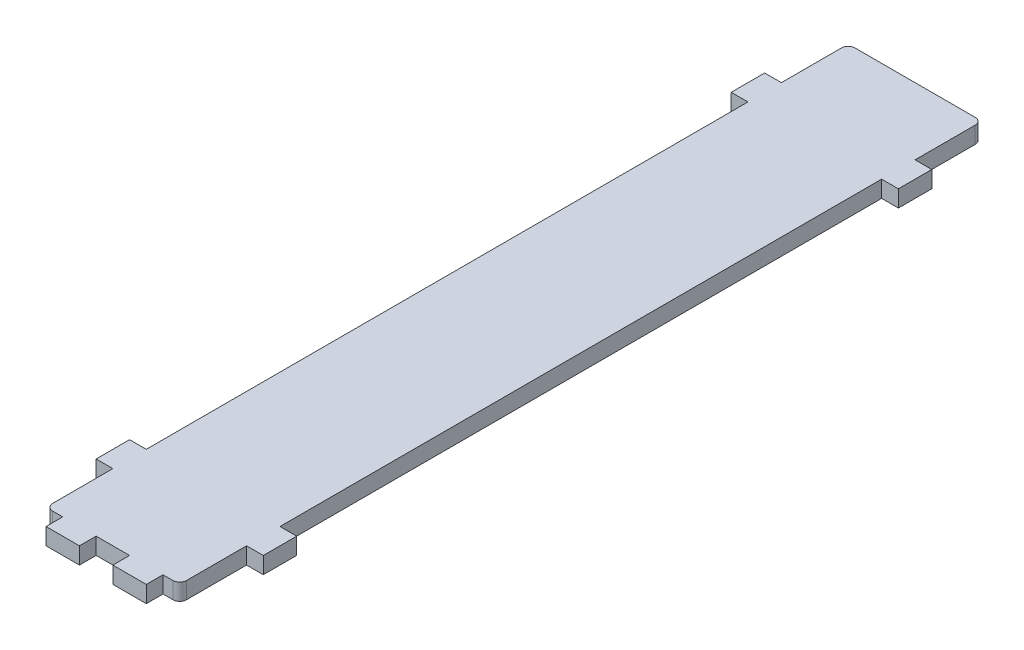
SolidWorks part; units mm, degrees
material "Beech"
ref_plane "Front Plane" through (0, 0, 0) normal (0, 0, 1) x (1, 0, 0)
ref_plane "Top Plane" through (0, 0, 0) normal (0, 1, 0) x (1, 0, 0)
ref_plane "Right Plane" through (0, 0, 0) normal (1, 0, 0) x (0, 0, -1)
sketch "Sketch1" plane through (0, 0, 0) normal (0, 1, 0) x (1, 0, 0)
  line L0 (0, 0) -> (6.35, 0)
  line L1 (6.35, 0) -> (6.35, -6.35)
  line L2 (6.35, -6.35) -> (19.05, -6.35)
  line L3 (19.05, -6.35) -> (19.05, 0)
  line L4 (19.05, 0) -> (31.75, 0)
  line L5 (31.75, 0) -> (31.75, -6.35)
  line L6 (31.75, -6.35) -> (44.45, -6.35)
  line L7 (44.45, -6.35) -> (44.45, 0)
  line L8 (44.45, 0) -> (50.8, 0)
  line L9 (50.8, 0) -> (50.8, 25.4)
  line L10 (50.8, 304.8) -> (0, 304.8)
  line L11 (0, 304.8) -> (0, 279.4)
  line L12 (50.8, 25.4) -> (57.15, 25.4)
  line L13 (57.15, 25.4) -> (57.15, 38.1)
  line L14 (57.15, 38.1) -> (50.8, 38.1)
  line L15 (50.8, 38.1) -> (50.8, 266.7)
  line L16 (50.8, 266.7) -> (57.15, 266.7)
  line L17 (57.15, 266.7) -> (57.15, 279.4)
  line L18 (57.15, 279.4) -> (50.8, 279.4)
  line L19 (50.8, 279.4) -> (50.8, 304.8)
  line L20 (0, 25.4) -> (-6.35, 25.4)
  line L22 (-6.35, 25.4) -> (-6.35, 38.1)
  line L23 (0, 38.1) -> (-6.35, 38.1)
  line L24 (0, 279.4) -> (-6.35, 279.4)
  line L25 (0, 25.4) -> (0, 0)
  line L26 (-6.35, 279.4) -> (-6.35, 266.7)
  line L27 (0, 266.7) -> (-6.35, 266.7)
  line L28 (0, 266.7) -> (0, 38.1)
  dimension "D1" = 12.7
  dimension "D2" = 6.35
  dimension "D3" = 25.4
  dimension "D4" = 25.4
  dimension "D5" = 6.35
  dimension "D6" = 304.8
  dimension "D7" = 50.8
  dimension "D8" = 25.4
  dimension "D9" = 6.35
extrude "Side Plate" add sketch "Sketch1" along normal blind 6.35
fillet "Fillet1" radius 2.54 4 edges at (50.8, 3.175, 0) (50.8, 3.175, -304.8) (0, 3.175, -304.8) (0, 3.175, 0)
equation "\"CageLeftBottomEdge\"=22.11mm"
equation "\"CageLeftTopEdge\"=22.11mm"
equation "\"CageRightBottomEdge\"=21.63mm"
equation "\"CageRightTopEdge\"=21.63mm"
equation "\"CageHeight\"=86.04mm"
equation "\"CageLength\"=73.76mm"
equation "\"CageTopScrewClearance\"=10mm"
equation "\"CageBottomScrewClearance\"=25mm"
equation "\"CageLeftTopDepth\"= 11.65mm"
equation "\"CageLeftBottomDepth\"=11.11mm"
equation "\"CageLeftTopHeight\"=8.56175mm"
equation "\"CageLeftBottomHeight\"=16mm"
equation "\"CageRightTopDepth\"= 11.05mm"
equation "\"CageRightBottomDepth\"=10.58mm"
equation "\"CageRightTopHeight\"=9.6mm"
equation "\"CageRightBottomHeight\"=15.49mm"
equation "\"CageLeftTopChannelDepth\"=2.41908mm"
equation "\"CageLeftBottomChannelDepth\"=2.588mm"
equation "\"CageLeftChannelHeight\"=11.7mm"
equation "\"CageRightTopChannelDepth\"=2.32mm"
equation "\"CageRightBottomChannelDepth\"=2.318mm"
equation "\"CageRightChannelHeight\"=10mm"
equation "\"CageChanRelHeight\"=23.99mm"
equation "\"CageChanRelDepth\"=5.492mm"
equation "\"CageChamberRadius\"=16.261mm"
equation "\"CageScrewDiameter\"=4.8mm"
equation "\"CageSetScrewDiameter\"=3.5mm"
equation "\"CageAxleRadius\"=6.639mm"
equation "\"CageAxleKeyHeight\"=1.619mm"
equation "\"CageAxleKeyWidth\"=2.662mm"
equation "\"CageHoseWindowWidth\"=16.29mm"
equation "\"CageHoseWindowHeight\"=26.5mm"
equation "\"CageHoseWindow-Edge\"=8.89mm"
equation "\"CageScrew-VerticalEdge\"=5.0mm"
equation "\"CageScrew-HorizontalEdge\"=7.5mm"
equation "\"CageScrew-HoseCornerScrewEdge\"=4.45mm"
equation "\"CageAxle-BottomEdge\"=56.05mm"
equation "\"CageAxle-FrontEdge\"=46.03mm"
equation "\"CageBackSetScrew-Axle\"=40mm"
equation "\"CageFrontSetScrew-Axle\"=22mm"
equation "\"CageVelocityWindow-BackEdge\"=34.8mm"
equation "\"CageVelocityWindow-BottomEdge\"=27.55mm"
equation "\"CageVelocityWindowHeight\"=22.29mm"
equation "\"CageVelocityWindowWidth\"=12.61mm"
equation "\"TriggerSlot-BottomEdge\"=6.35mm"
equation "\"TriggerSlot-FrontEdge\"=15mm"
equation "\"TriggerSlotSize\"=6.7mm"
equation "\"TriggerRackOffset\"=6mm"
equation "\"TriggerSlotSizeInt\"=.25in"
equation "\"MotorMountLegLength\"=.25in"
equation "\"GearOffset\"=.264907in"
equation "\"TriggerSlotSpacing\"=.25in"
equation "\"TriggerMiniSlotWidth\"=3.5mm"
equation "\"TriggerRackWidth\"=6.5mm"
equation "\"pandiscradius\"=14in"
equation "\"towermaterialwidth\"=.25in"
equation "\"towerslotlength\"=.5in"
equation "\"towermarkerspace\"=5in"
equation "\"towerslothorizoffset\"=1in"
equation "\"towerslothorizspacing\"=2in"
equation "\"towerslotvertoffset\"=3in"
equation "\"D1@Sketch1\"=\"towerslotlength\""
equation "\"D2@Sketch1\"=\"towermaterialwidth\""
equation "\"towerupslot\"=1in"
equation "\"D3@Sketch1\"=\"towerupslot\""
equation "\"towerslotvertspacing\"=1in"
equation "\"D4@Sketch1\"=\"towerslotvertspacing\""
equation "\"D5@Sketch1\"=\"towerslotlength\"/2"
equation "\"towerheight\"=12in"
equation "\"D6@Sketch1\"=\"towerheight\""
equation "\"D7@Sketch1\"=2*\"towerslotlength\"+\"towerslotvertspacing\""
equation "\"D8@Sketch1\"=\"towerupslot\""
equation "\"D9@Sketch1\"=\"towerslotvertoffset\"-(\"towermarkerspace\"/2)-\"towermaterialwidth\""
equation "\"D1@Side Plate\"=\"towermaterialwidth\""
equation "\"toweraxle\"=.5in"
equation "\"stepperouterrad\"=10mm"
equation "\"stepperscrewsize\"=3.45mm"
equation "\"stepperscrewc2c\"=49.5mm"
equation "\"stepperdepthoffset\"=24mm"
equation "\"stepperhorizoffset\"=22.91mm"
equation "\"shaftslotOD\"=18.8mm"
equation "\"shaftslotID\"=13.28mm"
equation "\"shaftkeywidth\"=2.67mm"
equation "\"shaftkeydepth\"=1.8mm"
equation "\"shaftcollartotaldepth\"=12.5mm"
equation "\"shaftsquaredepth\"=6mm"
equation "\"shaftsetscrewsize\"=3.5mm"
equation "\"shaftkeytightdepth\"=1.85mm"
equation "\"shaftslottightID\"=12.78mm"
equation "\"shaftsetscrewoffset\"=9mm"
equation "\"cagecollartotaldepth\"=10mm"
equation "\"cagecollartotalwidth\"=35mm"
equation "\"cagecollarbasedepth\"=4mm"
equation "\"gearhubintdiam\"=30mm"
equation "\"gearhubintwid\"=15mm"
equation "\"towerspeedwidth\"=2in"
equation "\"towerspeedheight\"=8in"
equation "\"towerspeedgap\"=2in"
equation "\"stepperaxleflat\"=.037in"
equation "\"stepperaxlerad\"=0.11811024in"
equation "\"ajaxaxlesize\"=3.87mm"
equation "\"ajaxinnercut\"=2.3mm"
equation "\"ajaxwidth\"=6.1mm"
equation "\"ajaxdiametral\"=25.8854"
equation "\"ajaxcutoutdepth\"=2.3mm"
equation "\"ajax4020gap\"=29.5mm"
equation "\"ajax4010gap\"=24.5mm"
equation "\"ajax20hubbuffer\"=6.1mm"
equation "\"ajax20hubholeoffset\"=.19685in"
equation "\"ajax20hubholesize\"=.059055in"
equation "\"ajax20cutoutint\"=13.4mm"
equation "\"ajax40hubholesize\"=7.21mm"
equation "\"ajax40hubholeoffset\"=10mm"
equation "\"ajax40hubbuffer\"=8.9mm"
equation "\"ajax40cutoutint\"=32.6mm"
equation "\"bearingpandiscrad\"=6.8in"
equation "\"bearingpandiscang\"=48.75deg"
equation "\"bearingclearholedist\"=4.7345in"
equation "\"bearingclearholesize\"=.5in"
equation "\"bearingclearholeang\"=22.5deg"
equation "\"bearingmountholedist\"=4.25in"
equation "\"bearingwirehole\"=1.5in"
equation "\"no6diam\"=.146in"
equation "\"shortconangle\"=20deg"
equation "\"shortconlen\"=.875in"
equation "\"longconlen\"=1.25in"
equation "\"longconangle\"=15deg"
